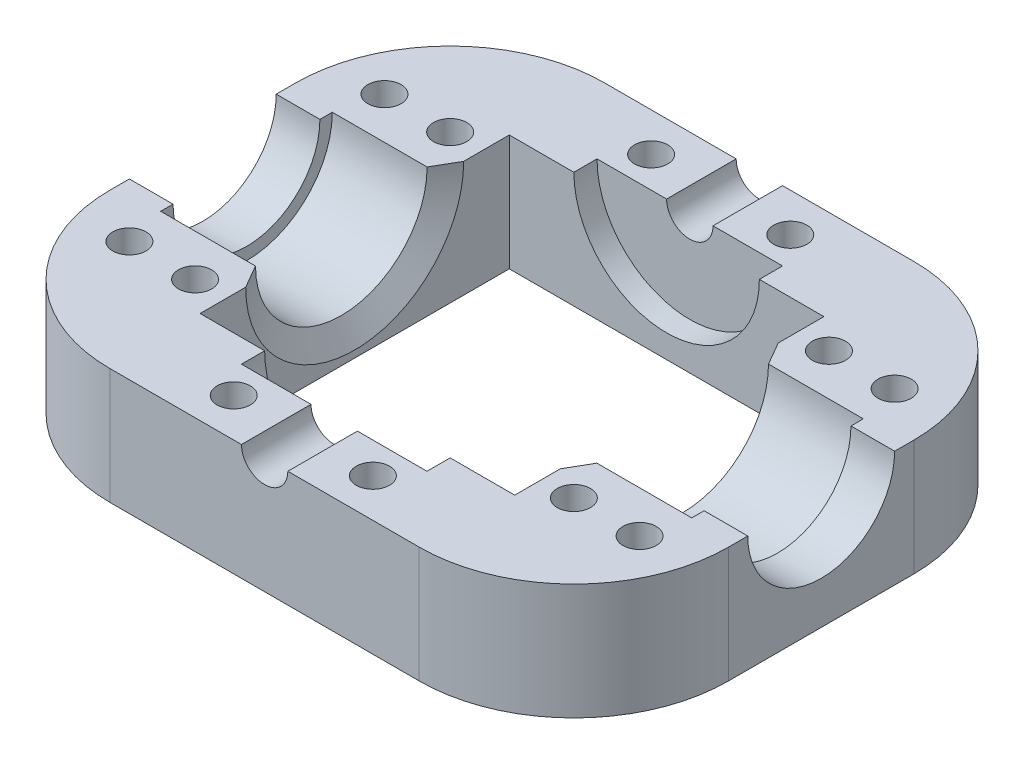
SolidWorks part; units mm, degrees
ref_plane "Спереди" through (0, 0, 0) normal (0, 0, 1) x (1, 0, 0)
ref_plane "Сверху" through (0, 0, 0) normal (0, 1, 0) x (1, 0, 0)
ref_plane "Справа" through (0, 0, 0) normal (1, 0, 0) x (0, 0, -1)
sketch "Sketch1" plane through (0, 0, 0) normal (0, 1, 0) x (1, 0, 0)
  line L1 (40, -32) -> (-40, -32)
  line L2 (40, -32) -> (40, 32)
  line L3 (40, 32) -> (-40, 32)
  line L4 (-40, -32) -> (-40, 32)
  line L5 (40, -32) -> (-40, 32) construction
  line L6 (40, 32) -> (-40, -32) construction
  line L7 (20.35, -20) -> (-20.35, -20)
  line L8 (20.35, -20) -> (20.35, 20)
  line L9 (20.35, 20) -> (-20.35, 20)
  line L10 (-20.35, -20) -> (-20.35, 20)
  line L11 (20.35, -20) -> (-20.35, 20) construction
  line L12 (20.35, 20) -> (-20.35, -20) construction
  point P0 (0, 0)
  point P6 (0, 0)
  dimension "D1" = 80
  dimension "D2" = 64
  dimension "D3" = 40
  dimension "D4" = 40.7
extrude "Boss-Extrude1" add sketch "Sketch1" along normal blind 15
sketch "Sketch3" plane through (0, 15, 0) normal (0, 1, 0) x (1, 0, 0)
  line L0 (-20.35, 0) -> (-40, 0) construction
  line L1 (-20.35, 20) -> (-20.35, -20) construction
  line L2 (-40, 32) -> (-40, -32) construction
  line L3 (20.35, 0) -> (40, 0) construction
  line L4 (20.35, -20) -> (20.35, 20) construction
  line L5 (40, -32) -> (40, 32) construction
  line L10 (20.35, -11.1) -> (34.35, -11.1)
  line L11 (20.35, -11.1) -> (20.35, 0)
  line L12 (20.35, 0) -> (34.35, 0)
  line L13 (34.35, -11.1) -> (34.35, 0)
  line L14 (20.35, -11.1) -> (34.35, 0) construction
  line L15 (20.35, 0) -> (34.35, -11.1) construction
  line L16 (-34.35, -11.1) -> (-20.35, -11.1)
  line L17 (-34.35, -11.1) -> (-34.35, 0)
  line L18 (-34.35, 0) -> (-20.35, 0)
  line L19 (-20.35, -11.1) -> (-20.35, 0)
  line L20 (-34.35, -11.1) -> (-20.35, 0) construction
  line L21 (-34.35, 0) -> (-20.35, -11.1) construction
  point P18 (27.35, -5.55)
  point P23 (-27.35, -5.55)
  dimension "D1" = 14
  dimension "D2" = 11.1
revolve "Cut-Revolve1" cut sketch "Sketch3" angle 360 about L12
sketch "Sketch4" plane through (40, 0, 0) normal (1, 0, 0) x (0, 0, -1)
  line L0 (-32, 15) -> (32, 15) construction
  circle A0 centre (0, 15) radius 9.5
  dimension "D1" = 19
extrude "Cut-Extrude2" cut sketch "Sketch4" against normal through all
sketch "Sketch5" plane through (0, 0, 32) normal (0, 0, 1) x (1, 0, 0)
  line L0 (-40, 15) -> (40, 15) construction
  circle A0 centre (0, 15) radius 3
  dimension "D1" = 6
extrude "Cut-Extrude3" cut sketch "Sketch5" against normal through all
sketch "Sketch8" plane through (0, 15, 0) normal (0, 1, 0) x (1, 0, 0)
  line L1 (-24.5, -16.5) -> (24.5, -16.5) construction
  line L2 (-24.5, -16.5) -> (-24.5, 16.5) construction
  line L3 (-24.5, 16.5) -> (24.5, 16.5) construction
  line L4 (24.5, -16.5) -> (24.5, 16.5) construction
  line L5 (-24.5, -16.5) -> (24.5, 16.5) construction
  line L6 (-24.5, 16.5) -> (24.5, -16.5) construction
  line L7 (-9, 27) -> (9, 27) construction
  line L8 (-9, 27) -> (-9, -27) construction
  line L9 (-9, -27) -> (9, -27) construction
  line L10 (9, 27) -> (9, -27) construction
  line L11 (-9, 27) -> (9, -27) construction
  line L12 (-9, -27) -> (9, 27) construction
  line L13 (33, -16.5) -> (-33, -16.5) construction
  line L14 (33, -16.5) -> (33, 16.5) construction
  line L15 (33, 16.5) -> (-33, 16.5) construction
  line L16 (-33, -16.5) -> (-33, 16.5) construction
  line L17 (33, -16.5) -> (-33, 16.5) construction
  line L18 (33, 16.5) -> (-33, -16.5) construction
  circle A0 centre (24.5, 16.5) radius 2.15
  circle A1 centre (24.5, -16.5) radius 2.15
  circle A2 centre (-24.5, -16.5) radius 2.15
  circle A3 centre (-24.5, 16.5) radius 2.15
  circle A4 centre (9, -27) radius 2.15
  circle A5 centre (-9, -27) radius 2.15
  circle A6 centre (-9, 27) radius 2.15
  circle A7 centre (9, 27) radius 2.15
  circle A8 centre (-33, 16.5) radius 2.15
  circle A9 centre (33, 16.5) radius 2.15
  circle A10 centre (33, -16.5) radius 2.15
  circle A11 centre (-33, -16.5) radius 2.15
  circle A12 centre (-24.5, 16.5) radius 4 construction
  circle A13 centre (-33, 16.5) radius 4 construction
  point P0 (0, 0)
  point P10 (0, 0)
  point P16 (0, 0)
  dimension "D3" = 4.3
  dimension "D7" = 8
  dimension "D1" = 33
  dimension "D2" = 49
  dimension "D4" = 18
  dimension "D5" = 54
  dimension "D6" = 66
extrude "Cut-Extrude6" cut sketch "Sketch8" against normal through all
fillet "Fillet1" radius 20 4 edges at (-40, 7.5, 32) (-40, 7.5, -32) (40, 7.5, -32) (40, 7.5, 32)
chamfer "Chamfer1" distance 3 angle 30 2 edges at (-20.35, 3.9, 0) (20.35, 3.9, 0)
sketch "Sketch9" plane through (0, 15, 0) normal (0, 1, 0) x (1, 0, 0)
  line L0 (0, 29.8714) -> (0, -31.0419) construction
  line L1 (-3, 20) -> (-20.35, 20) construction
  line L2 (-12, -23) -> (0, -23)
  line L3 (-12, -23) -> (-12, -20)
  line L4 (-12, -20) -> (0, -20)
  line L5 (0, -23) -> (0, -20)
  line L6 (-12, -23) -> (0, -20) construction
  line L7 (-12, -20) -> (0, -23) construction
  line L8 (-12, 20) -> (0, 20)
  line L9 (-12, 20) -> (-12, 23)
  line L10 (-12, 23) -> (0, 23)
  line L11 (0, 20) -> (0, 23)
  line L12 (-12, 20) -> (0, 23) construction
  line L13 (-12, 23) -> (0, 20) construction
  line L14 (-20.35, -20) -> (-3, -20) construction
  point P3 (-6, -21.5)
  point P8 (-6, 21.5)
  dimension "D1" = 3
  dimension "D2" = 12
revolve "Cut-Revolve2" cut sketch "Sketch9" angle 360 about L0
